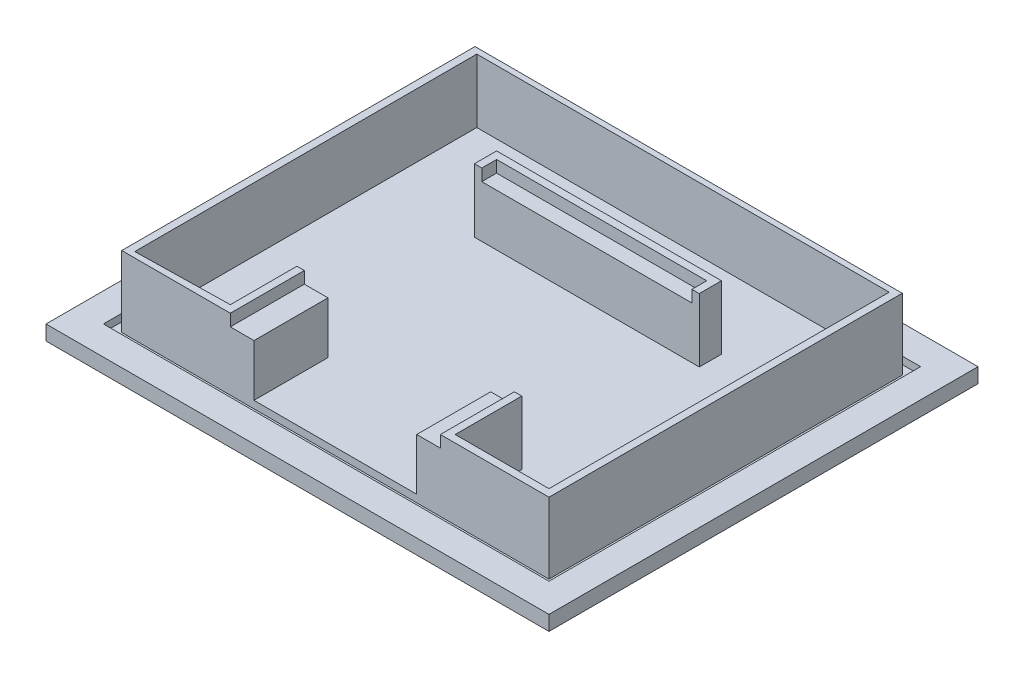
SolidWorks part; units mm, degrees
ref_plane "Front Plane" through (0, 0, 0) normal (0, 0, 1) x (1, 0, 0)
ref_plane "Top Plane" through (0, 0, 0) normal (0, 1, 0) x (1, 0, 0)
ref_plane "Right Plane" through (0, 0, 0) normal (1, 0, 0) x (0, 0, -1)
sketch "Sketch1" plane through (0, 0, 0) normal (0, 1, 0) x (1, 0, 0)
  line L0 (-85, -72.5) -> (-85, 72.5)
  line L1 (0, 0) -> (85, 0) construction
  line L2 (0, 0) -> (0, 72.5) construction
  line L3 (-85, 72.5) -> (85, 72.5)
  line L4 (85, -72.5) -> (85, 72.5)
  line L5 (-85, -72.5) -> (85, -72.5)
  point P9 (-85, 0)
  dimension "D1" = 170
  dimension "D2" = 145
extrude "Boss-Extrude1" add sketch "Sketch1" along normal blind 5
sketch "Sketch2" plane through (0, 5, 0) normal (0, 1, 0) x (1, 0, 0)
  line L0 (85, 72.5) -> (-85, 72.5) construction
  line L1 (0, 0) -> (75.3, 0) construction
  line L2 (0, 0) -> (0, 62.8) construction
  line L3 (-75.3, 62.8) -> (75.3, 62.8)
  line L4 (75.3, -62.8) -> (75.3, 62.8)
  line L5 (85, -72.5) -> (85, 72.5) construction
  line L6 (-75.3, -62.8) -> (-75.3, 62.8)
  line L7 (-75.3, -62.8) -> (75.3, -62.8)
  line L8 (-72.2, 59.7) -> (72.2, 59.7)
  line L9 (72.2, 59.7) -> (72.2, -59.7)
  line L10 (-72.2, 59.7) -> (-72.2, -59.7)
  line L11 (-72.2, -59.7) -> (72.2, -59.7)
  point P12 (-75.3, 0)
  point P17 (72.2, 0)
  point P18 (0, 59.7)
  point P20 (-72.2, 0)
  dimension "D1" = 9.7
  dimension "D2" = 9.7
  dimension "D3" = 3.1
  dimension "D4" = 3.1
extrude "Cut-Extrude1" cut sketch "Sketch2" against normal blind 2.5
sketch "Sketch4" plane through (0, 5, 0) normal (0, 1, 0) x (1, 0, 0)
  line L2 (0, -57.8) -> (0, 30.3) construction
  line L5 (35.5, -59.7) -> (35.5, 30.3) construction
  line L6 (35.5, -59.7) -> (-35.5, -59.7) construction
  line L7 (0, -59.7) -> (0, 30.3) construction
  line L8 (35.5, 30.3) -> (-35.5, 30.3) construction
  line L9 (-35.5, -59.7) -> (-35.5, 30.3) construction
  line L10 (-72.2, -59.7) -> (72.2, -59.7) construction
  line L11 (-72.2, -59.7) -> (72.2, -59.7) construction
  line L12 (38, -59.7) -> (0, -59.7)
  line L13 (38, -59.7) -> (38, 32.8)
  line L14 (38, 32.8) -> (-38, 32.8)
  line L16 (-38, -59.7) -> (-38, 32.8)
  point P16 (0, 32.8)
  point P17 (0, 0)
  dimension "D1" = 71
  dimension "D2" = 90
  dimension "D3" = 2.5
  dimension "D4" = 2.5
sketch "Sketch5" plane through (0, 5, 0) normal (0, 1, 0) x (1, 0, 0)
  line L0 (35.5, -59.7) -> (35.5, 30.3) construction
  line L5 (35.5, 25.3) -> (-35.5, 25.3)
  line L6 (35.5, 25.3) -> (35.5, 32.8)
  line L7 (35.5, 32.8) -> (-35.5, 32.8)
  line L8 (-35.5, 25.3) -> (-35.5, 32.8)
  line L9 (-35.5, -59.7) -> (-35.5, 30.3) construction
  line L10 (38, 32.8) -> (-38, 32.8) construction
  line L11 (35.5, 30.3) -> (-35.5, 30.3) construction
  line L12 (0, 30.3) -> (0, 12.171) construction
  line L13 (-35.5, -59.7) -> (-27.5, -59.7)
  line L14 (-35.5, -59.7) -> (-35.5, -34.7)
  line L15 (-35.5, -34.7) -> (-27.5, -34.7)
  line L16 (-27.5, -59.7) -> (-27.5, -34.7)
  line L17 (35.5, -34.7) -> (27.5, -34.7)
  line L18 (27.5, -59.7) -> (27.5, -34.7)
  line L19 (35.5, -59.7) -> (27.5, -59.7)
  line L20 (35.5, -59.7) -> (35.5, -34.7)
  dimension "D1" = 5
  dimension "D2" = 8
  dimension "D3" = 25
extrude "Boss-Extrude2" add sketch "Sketch5" along normal blind 17.5
sketch "Sketch6" plane through (0, 5, 0) normal (0, 1, 0) x (1, 0, 0)
  line L0 (-35.5, 25.3) -> (35.5, 25.3) construction
  line L1 (35.5, 25.3) -> (38, 25.3)
  line L2 (35.5, 25.3) -> (35.5, 32.8)
  line L3 (35.5, 32.8) -> (38, 32.8)
  line L4 (38, 25.3) -> (38, 32.8)
  line L5 (0, 32.8) -> (0, 0) construction
  line L6 (-35.5, 32.8) -> (-38, 32.8)
  line L7 (-38, 25.3) -> (-38, 32.8)
  line L8 (-35.5, 25.3) -> (-38, 25.3)
  line L9 (-35.5, 25.3) -> (-35.5, 32.8)
  line L10 (35.5, 25.3) -> (35.5, 32.8) construction
  line L11 (38, -34.7) -> (35.5, -34.7)
  line L12 (-38, -59.7) -> (-35.5, -59.7)
  line L13 (-38, -59.7) -> (-38, -34.7)
  line L14 (-38, -34.7) -> (-35.5, -34.7)
  line L15 (-35.5, -59.7) -> (-35.5, -34.7)
  line L16 (35.5, -59.7) -> (35.5, -34.7)
  line L17 (38, -59.7) -> (35.5, -59.7)
  line L18 (38, -59.7) -> (38, -34.7)
  dimension "D1" = 25
extrude "Boss-Extrude3" add sketch "Sketch6" along normal blind 21.5
sketch "Sketch7" plane through (0, 22.5, 0) normal (0, 1, 0) x (1, 0, 0)
  line L1 (35.5, 32.8) -> (-35.5, 32.8)
  line L2 (35.5, 32.8) -> (35.5, 30.3)
  line L3 (35.5, 30.3) -> (-35.5, 30.3)
  line L4 (-35.5, 32.8) -> (-35.5, 30.3)
  dimension "D1" = 2.5
extrude "Boss-Extrude4" add sketch "Sketch7" along normal blind 4
sketch "Sketch9" plane through (0, 5, 0) normal (0, 1, 0) x (1, 0, 0)
  line L2 (72.2, -59.7) -> (72.2, 60.3)
  line L4 (69.7, -57.2) -> (69.7, 57.8)
  line L5 (0, 0) -> (0, -29.0575) construction
  line L7 (-69.7, -57.8) -> (-69.7, 57.8)
  line L9 (-72.2, -59.7) -> (-72.2, 60.3)
  line L10 (38, -59.7) -> (38, -34.7) construction
  line L11 (-72.2, 60.3) -> (72.2, 60.3)
  line L12 (-72.2, 60.3) -> (-72.2, 57.8)
  line L13 (-69.7, 57.8) -> (69.7, 57.8)
  line L14 (72.2, 60.3) -> (72.2, 57.8)
  line L15 (72.2, -59.7) -> (38, -59.7)
  line L16 (72.2, -59.7) -> (72.2, -57.8)
  line L17 (69.7, -57.2) -> (38, -57.2)
  line L18 (38, -59.7) -> (38, -57.2)
  line L19 (-69.7, -57.8) -> (-38, -57.2)
  line L20 (-38, -59.7) -> (-38, -57.2)
  line L21 (-72.2, -59.7) -> (-38, -59.7)
  line L22 (-72.2, -59.7) -> (-72.2, -57.8)
  point P1 (0, 0)
  point P3 (0, 0)
  line M16 (38, -34.7) -> (38, -59.7)
  line M17 (38, -59.7) -> (72.2, -59.7)
  line M18 (72.2, -59.7) -> (72.2, 59.7)
  line M19 (72.2, 59.7) -> (-72.2, 59.7)
  line M20 (-72.2, 59.7) -> (-72.2, -59.7)
  line M21 (-72.2, -59.7) -> (-38, -59.7)
  line M22 (-38, -59.7) -> (-38, -34.7)
  dimension "D1" = 2.5
  dimension "D2" = 2.5
  dimension "D3" = 2.5
extrude "Boss-Extrude6" add sketch "Sketch9" along normal blind 21.5 contours L19 L7 L13 L4 L17 L2 L9 M16 M17 M18 M19 M20 M21 M22
